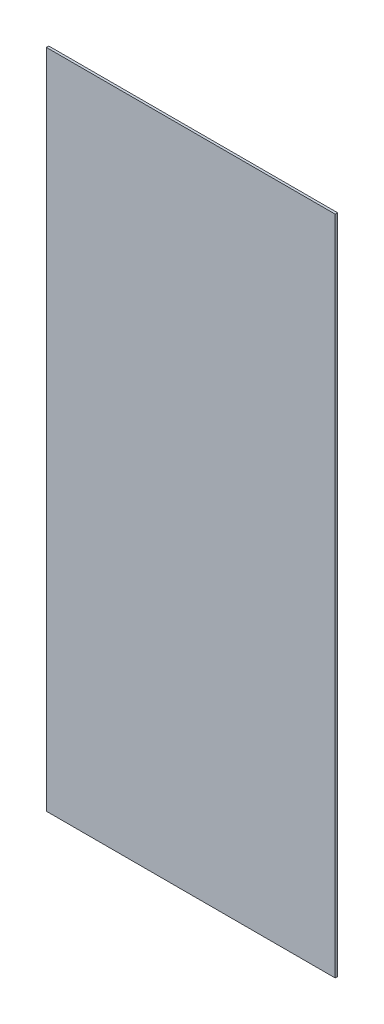
SolidWorks part; units mm, degrees
ref_plane "정면" through (0, 0, 0) normal (0, 0, 1) x (1, 0, 0)
ref_plane "윗면" through (0, 0, 0) normal (0, 1, 0) x (1, 0, 0)
ref_plane "우측면" through (0, 0, 0) normal (1, 0, 0) x (0, 0, -1)
sketch "스케치1" plane through (0, 0, 0) normal (0, 0, 1) x (1, 0, 0)
  line L1 (0, 0) -> (358, 0)
  line L2 (0, 0) -> (0, 820)
  line L3 (0, 820) -> (358, 820)
  line L4 (358, 0) -> (358, 820)
  dimension "D1" = 358
  dimension "D2" = 820
extrude "보스-돌출1" add sketch "스케치1" along normal blind 3
